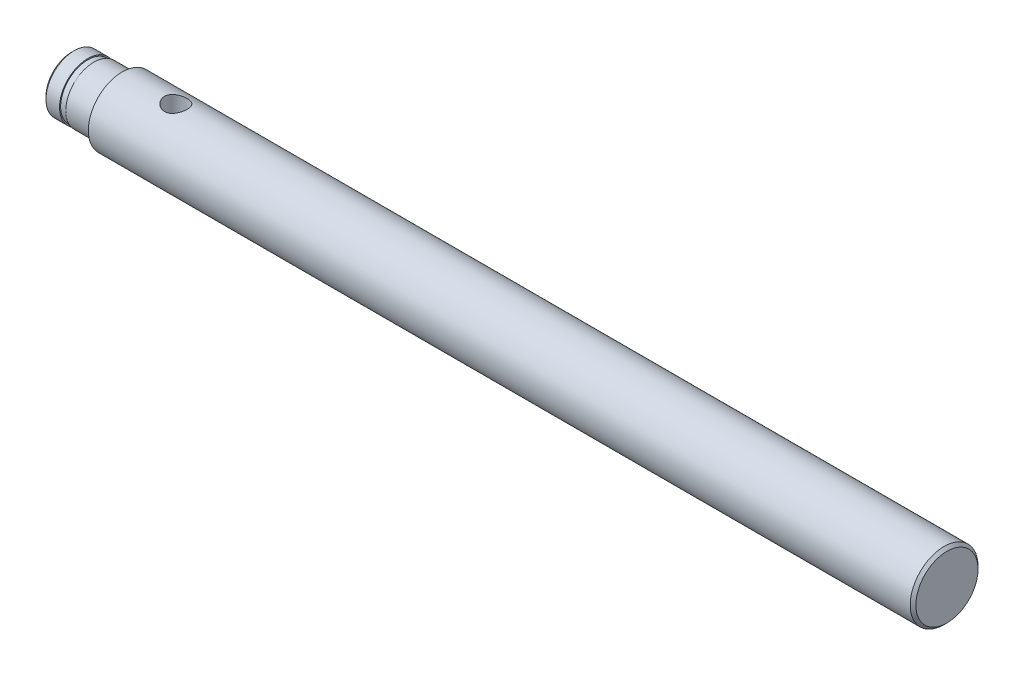
SolidWorks part; units mm, degrees
material "Stainless Steel (ferritic)"
ref_plane "Front Plane" through (0, 0, 0) normal (0, 0, 1) x (1, 0, 0)
ref_plane "Top Plane" through (0, 0, 0) normal (0, 1, 0) x (1, 0, 0)
ref_plane "Right Plane" through (0, 0, 0) normal (1, 0, 0) x (0, 0, -1)
sketch "Sketch1" plane through (0, 0, 0) normal (1, 0, 0) x (0, 0, -1)
  circle A0 centre (0, 0) radius 6
  dimension "D1" = 12
extrude "Boss-Extrude1" add sketch "Sketch1" along normal blind 155
sketch "Sketch2" plane through (0, 0, 0) normal (0, 0, 1) x (1, 0, 0)
  line L0 (0, 5) -> (0, 6)
  line L1 (0, 6) -> (9, 6)
  line L2 (9, 6) -> (9, 5)
  line L3 (9, 5) -> (4, 5)
  line L4 (4, 5) -> (4, 4.8)
  line L5 (4, 4.8) -> (2.9, 4.8)
  line L6 (2.9, 4.8) -> (2.9, 5)
  line L7 (2.9, 5) -> (0, 5)
  line L10 (155, 6) -> (0, 6) construction
  dimension "D1" = 5
  dimension "D2" = 1.1
  dimension "D3" = 4.8
  dimension "D4" = 5
  dimension "D5" = 2.9
ref_axis "Axis1" through (155, 0, 0) along (-1, 0, 0)
revolve "Cut-Revolve1" cut sketch "Sketch2" angle 360 about axis through (155, 0, 0) along (-1, 0, 0)
sketch "Sketch3" plane through (0, 0, 0) normal (0, 1, 0) x (1, 0, 0)
  line L0 (155, 0) -> (0, 0) construction
  circle A0 centre (18.5, 0) radius 2
  dimension "D1" = 4
  dimension "D2" = 18.5
extrude "Cut-Extrude1" cut sketch "Sketch3" against normal mid plane 20
chamfer "Chamfer1" distance 0.5 angle 45 2 edges at (0, 0, -5) (155, 0, -6)
fillet "Fillet1" radius 0.3 1 edges at (9, 0, -5)
